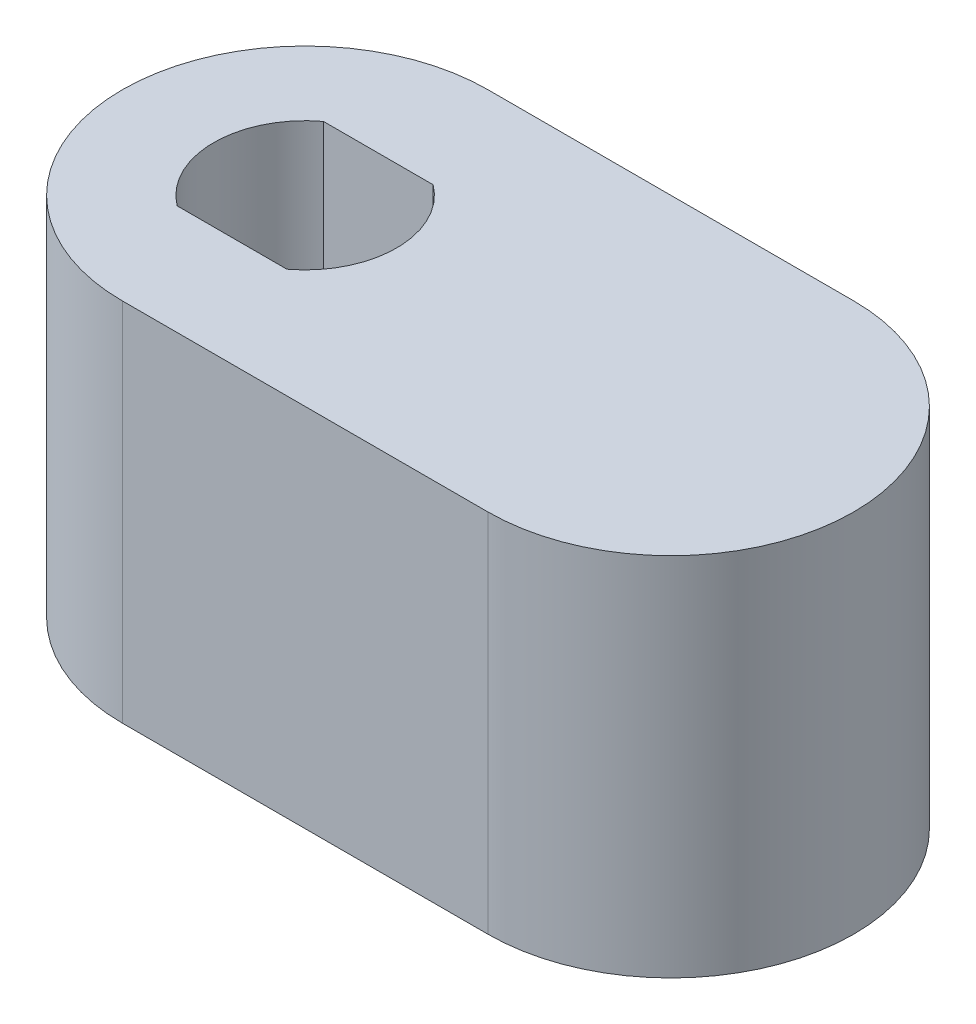
SolidWorks part; units mm, degrees
ref_plane "前视基准面" through (0, 0, 0) normal (0, 0, 1) x (1, 0, 0)
ref_plane "上视基准面" through (0, 0, 0) normal (0, 1, 0) x (1, 0, 0)
ref_plane "右视基准面" through (0, 0, 0) normal (1, 0, 0) x (0, 0, -1)
other "Configuration Table"
sketch "草图1" plane through (0, 0, 0) normal (0, 1, 0) x (1, 0, 0)
  line L0 (0, 0) -> (10, 0) construction
  line L1 (0, 5) -> (10, 5)
  line L2 (0, -5) -> (10, -5)
  arc A0 (0, 5) -> (0, -5) centre (0, 0) ccw
  arc A1 (10, -5) -> (10, 5) centre (10, 0) ccw
  point P3 (5, 0)
  dimension "D1" = 10
  dimension "D2" = 10
extrude "凸台-拉伸1" add sketch "草图1" along normal blind 10
sketch "草图2" plane through (0, 10, 0) normal (0, 1, 0) x (1, 0, 0)
  line L0 (-1.5, 2) -> (1.5, 2)
  line L1 (-1.5, -2) -> (1.5, -2)
  line L2 (-2.5, 0) -> (2.5, 0) construction
  circle A0 centre (0, 0) radius 2.5
  dimension "D1" = 5
  dimension "D2" = 4
sketch "草图5" plane through (0, 10, 0) normal (0, 1, 0) x (1, 0, 0)
extrude "切除-拉伸1" cut sketch "草图2" against normal blind 4 contours L2 A0 L1 | A0 L2 L0
hole_wizard "M3 六角凹锥坑螺钉的锥形沉头孔1" positions "草图6" profile "草图7" countersink size "M3" standard "ISO"
sketch "草图6" plane through (0, 0, 0) normal (0, -1, 0) x (-1, 0, 0)
  point P0 (0, 0)
sketch "草图7" plane through (0, 0, 0) normal (1, 0, 0) x (0, 0, -1)
  line L0 (0, 0) -> (0, 9.1215)
  line L1 (0, 9.1215) -> (1.7, 8.1)
  line L2 (1.7, 8.1) -> (1.7, 1.66)
  line L3 (1.7, 1.66) -> (3.36, 0)
  line L5 (3.36, 0) -> (0, 0)
  line L6 (-1.7, 1.66) -> (-3.36, 0) construction
  line L10 (0, 9.1215) -> (-1.7, 8.1) construction
  line L11 (0, -6.35) -> (0, 107.95) construction
  dimension "孔直径" = 3.4
  dimension "孔深度" = 8.1
  dimension "近端锥形沉头孔直径" = 6.72
  dimension "近端锥形沉头孔角度" = 90
  dimension "导头角度" = 118
hole_wizard "孔1" positions "草图8" profile "草图9" legacy
sketch "草图8" plane through (0, 0, 0) normal (0, -1, 0) x (-1, 0, 0)
  point P0 (-10, 0)
sketch "草图9" plane through (10, 0, 0) normal (1, 0, 0) x (0, 0, -1)
  line L0 (0, 0) -> (0, 7.5)
  line L1 (0, 7.5) -> (2.075, 7.5)
  line L2 (2.075, 7.5) -> (2.075, 0)
  line L3 (2.075, 0) -> (0, 0)
  line L4 (0, 110) -> (0, -10) construction
  dimension "直径" = 4.15
  dimension "深度" = 7.5
